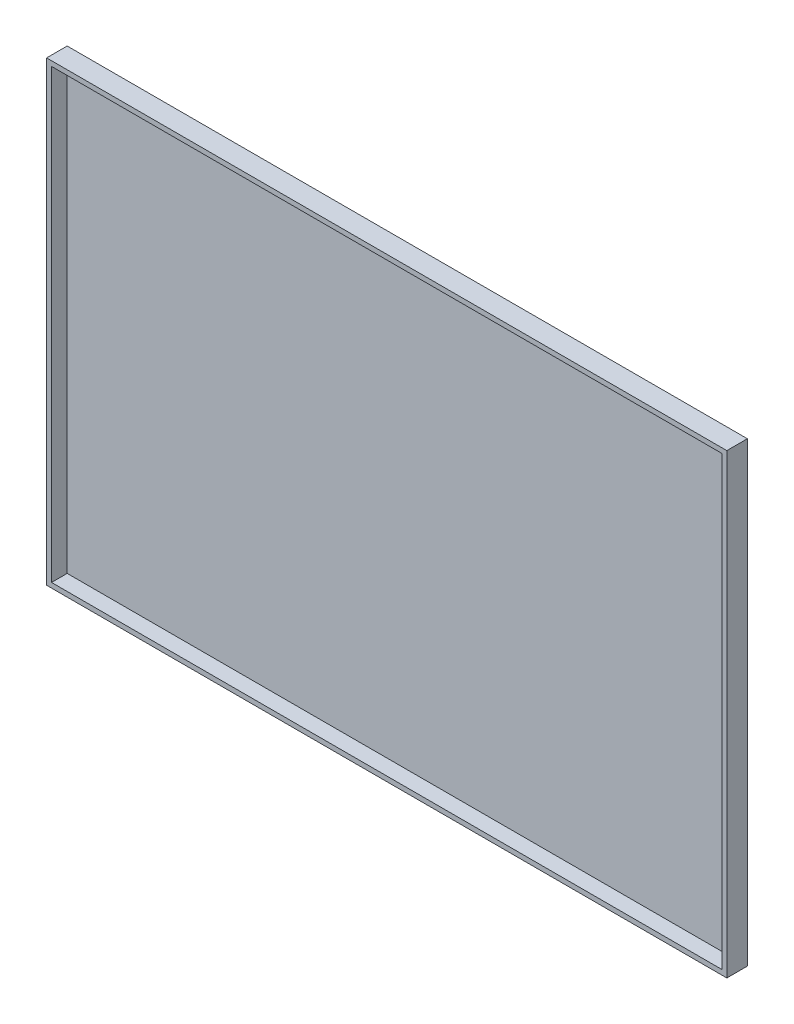
SolidWorks part; units mm, degrees
ref_plane "Front Plane" through (0, 0, 0) normal (0, 0, 1) x (1, 0, 0)
ref_plane "Top Plane" through (0, 0, 0) normal (0, 1, 0) x (1, 0, 0)
ref_plane "Right Plane" through (0, 0, 0) normal (1, 0, 0) x (0, 0, -1)
sketch "Esquisse1" plane through (0, 0, 0) normal (0, 0, 1) x (1, 0, 0)
  line L1 (-1500, 1000) -> (1500, 1000)
  line L2 (-1500, 1000) -> (-1500, -1000)
  line L3 (-1500, -1000) -> (1500, -1000)
  line L4 (1500, 1000) -> (1500, -1000)
  point P4 (0, 1000)
  point P6 (-1500, 0)
  dimension "D1" = 2000
  dimension "D2" = 3000
extrude "Bottom" add sketch "Esquisse1" along normal blind 22
sketch "Esquisse2" plane through (0, 0, 0) normal (0, 0, -1) x (-1, 0, 0)
  line L0 (1500, -1000) -> (-1500, -1000) construction
  line L1 (-1522, 1022) -> (1522, 1022)
  line L2 (-1522, 1022) -> (-1522, -1022)
  line L3 (-1522, -1022) -> (1522, -1022)
  line L4 (1522, 1022) -> (1522, -1022)
  line L5 (1500, 1000) -> (-1500, 1000)
  line L6 (1500, 1000) -> (1500, -1000)
  line L7 (1500, -1000) -> (-1500, -1000)
  line L8 (-1500, 1000) -> (-1500, -1000)
  point P11 (-1500, -1000)
  dimension "D1" = 22
  dimension "D2" = 22
  dimension "D3" = 22
  dimension "D4" = 22
extrude "Border" add sketch "Esquisse2" against normal blind 92 separate body
